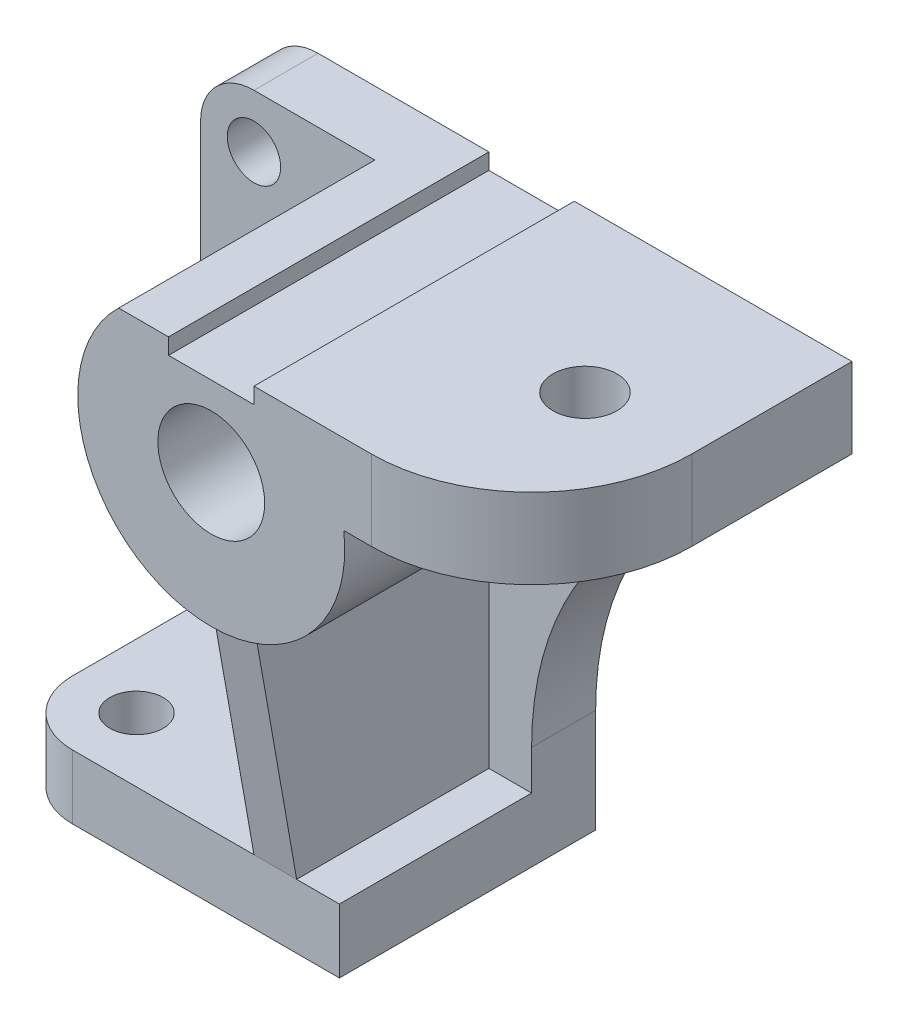
SolidWorks part; units mm, degrees
material "Plain Carbon Steel"
ref_plane "Front Plane" through (0, 0, 0) normal (0, 0, 1) x (1, 0, 0)
ref_plane "Top Plane" through (0, 0, 0) normal (0, 1, 0) x (1, 0, 0)
ref_plane "Right Plane" through (0, 0, 0) normal (1, 0, 0) x (0, 0, -1)
sketch "Sketch1" plane through (0, 0, 0) normal (0, 0, 1) x (1, 0, 0)
  line L0 (10, 100) -> (110, 100)
  line L1 (110, 100) -> (110, 85)
  line L2 (110, 85) -> (95, 85)
  line L3 (95, 85) -> (95, 73)
  line L4 (0, 90) -> (0, 0)
  line L5 (0, 0) -> (62, 0)
  line L6 (62, 0) -> (62, 19.4183)
  arc A0 (62, 19.4183) -> (95, 73) centre (122, 19.4183) cw
  arc A1 (10, 100) -> (0, 90) centre (10, 90) ccw
  circle A2 centre (10, 90) radius 5
  point P12 (0, 100)
  dimension "D8" = 10
  dimension "D6" = 60
  dimension "D9" = 10
  dimension "D1" = 100
  dimension "D2" = 110
  dimension "D3" = 15
  dimension "D4" = 15
  dimension "D5" = 12
  dimension "D7" = 62
extrude "Boss-Extrude1" add sketch "Sketch1" along normal blind 12
sketch "Sketch2" plane through (0, 0, 0) normal (0, -1, 0) x (1, 0, 0)
  line L0 (62, 12) -> (62, 48)
  line L1 (62, 48) -> (12, 48)
  line L2 (0, 12) -> (0, 36)
  line L4 (0, 12) -> (62, 12)
  line L5 (0, 0) -> (62, 0) construction
  arc A0 (12, 48) -> (0, 36) centre (12, 36) ccw
  circle A1 centre (12, 36) radius 5
  dimension "D2" = 12
  dimension "D3" = 10
  dimension "D1" = 48
extrude "Boss-Extrude2" add sketch "Sketch2" against normal blind 12
sketch "Sketch5" plane through (0, 0, 12) normal (0, 0, 1) x (1, 0, 0)
  line L0 (110, 100) -> (10, 100) construction
  line L3 (32.6506, 100) -> (110, 100)
  line L4 (110, 100) -> (110, 85)
  line L5 (110, 85) -> (74.8193, 85)
  arc A0 (32.6506, 100) -> (74.8193, 85) centre (50, 82) ccw
  dimension "D1" = 50
  dimension "D2" = 18
  dimension "D3" = 60
extrude "Boss-Extrude3" add sketch "Sketch5" along normal blind 48
sketch "Sketch6" plane through (0, 0, 60) normal (0, 0, 1) x (1, 0, 0)
  circle A1 centre (50, 82) radius 10
  dimension "D1" = 20
fillet "Fillet1" radius 30 1 edges at (110, 92.5, 60)
extrude "Cut-Extrude1" cut sketch "Sketch6" against normal through all
sketch "Sketch7" plane through (0, 0, 60) normal (0, 0, 1) x (1, 0, 0)
  line L4 (50, 82) -> (50, 105.3965) construction
  line L6 (80, 100) -> (32.6506, 100) construction
  line L7 (42, 100) -> (58, 100)
  line L8 (42, 100) -> (42, 97)
  line L9 (42, 97) -> (58, 97)
  line L10 (58, 100) -> (58, 97)
  dimension "D1" = 16
  dimension "D2" = 3
extrude "Cut-Extrude2" cut sketch "Sketch7" against normal through all
sketch "Sketch9" plane through (0, 100, 0) normal (0, 1, 0) x (1, 0, 0)
  line L0 (110, 0) -> (58, 0) construction
  line L2 (110, -30) -> (110, 0) construction
  circle A0 centre (90, -30) radius 6
  dimension "D1" = 12
  dimension "D2" = 30
  dimension "D3" = 20
extrude "Cut-Extrude3" cut sketch "Sketch9" against normal up to next contours A0
ref_plane "Plane1" through (50, 0, 0) normal (1, 0, 0) x (0, 0, -1)
sketch "Sketch8" plane through (50, 0, 0) normal (1, 0, 0) x (0, 0, -1)
  line L0 (-48, 12) -> (-55.9347, 57)
  line L1 (-60, 57) -> (-12, 57) construction
  line L3 (-12, 12) -> (-48, 12) construction
  dimension "D1" = 100
rib "Rib9" sketch "Sketch8" sketch "Sketch8" thickness 8 extrusion direction parallel to sketch draft on no parameters "D1"=8
